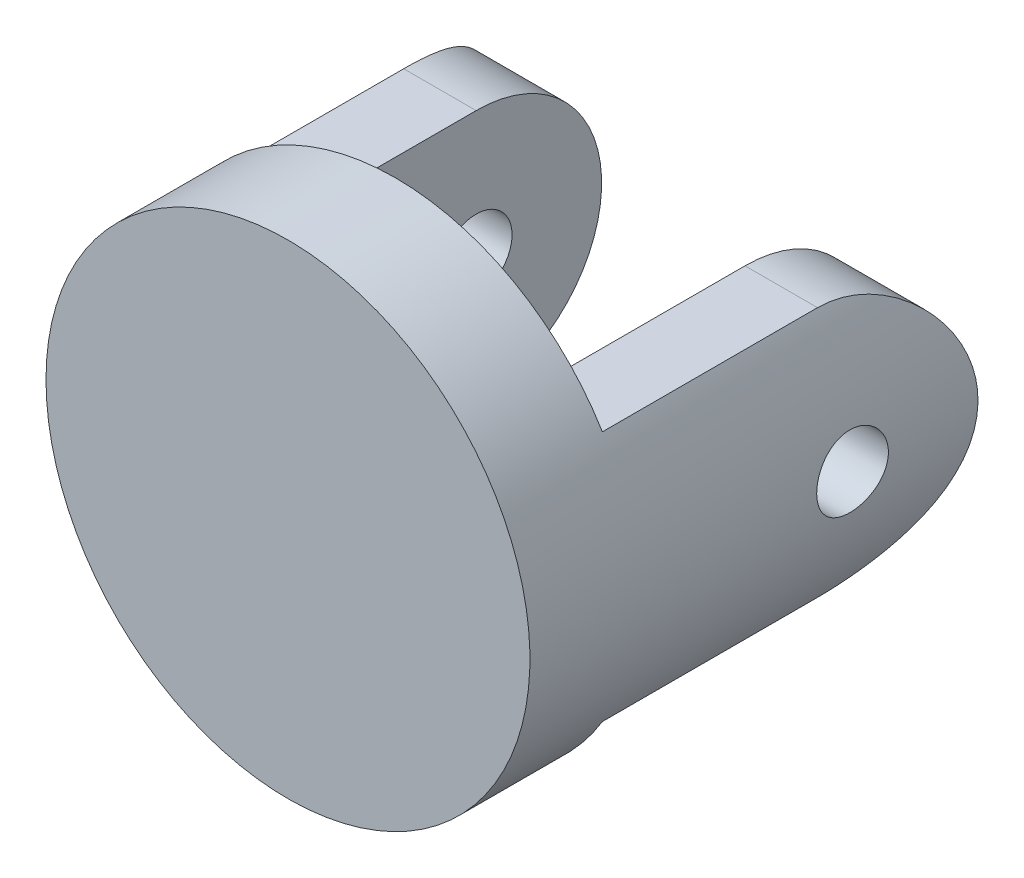
SolidWorks part; units mm, degrees
ref_plane "Front Plane" through (0, 0, 0) normal (0, 0, 1) x (1, 0, 0)
ref_plane "Top Plane" through (0, 0, 0) normal (0, 1, 0) x (1, 0, 0)
ref_plane "Right Plane" through (0, 0, 0) normal (1, 0, 0) x (0, 0, -1)
sketch "Sketch2" plane through (0, 0, 0) normal (0, 0, -1) x (-1, 0, 0)
  circle A0 centre (0, 0) radius 6.75
  dimension "D1" = 13.5
extrude "U Joint Base" add sketch "Sketch2" along normal blind 3
sketch "Sketch3" plane through (0, 0, -3) normal (0, 0, -1) x (-1, 0, 0)
  line L0 (-5.7717, 3.5) -> (-3.75, 3.5)
  line L1 (-3.75, 3.5) -> (-3.75, -3.5)
  line L2 (-3.75, -3.5) -> (-5.7717, -3.5)
  line L3 (3.75, -3.5) -> (3.75, 3.5)
  line L4 (3.75, 3.5) -> (5.7717, 3.5)
  line L5 (5.7717, -3.5) -> (3.75, -3.5)
  circle A0 centre (0, 0) radius 6.75 construction
  arc A1 (-5.7717, -3.5) -> (-5.7717, 3.5) centre (0, 0) cw
  arc A2 (5.7717, 3.5) -> (5.7717, -3.5) centre (0, 0) cw
  point P4 (-3.957, -3.4942)
  point P16 (0, 0)
  dimension "D2" = 7.5
  dimension "D3" = 7
  dimension "D1" = 2
extrude "U Joint Standups" add sketch "Sketch3" along normal blind 9.5
sketch "Sketch4" plane through (0, 0, 0) normal (1, 0, 0) x (0, 0, -1)
  line L0 (12.5, 3.5) -> (3, 3.5) construction
  line L1 (12.5, -3.5) -> (12.5, 3.5) construction
  line L2 (9, -3.5) -> (12.5, -3.5)
  line L3 (12.5, -3.5) -> (12.5, 0)
  line L4 (12.5, 0) -> (12.5, 3.5)
  line L5 (12.5, 3.5) -> (9, 3.5)
  line L6 (12.5, -3.5) -> (3, -3.5) construction
  arc A0 (12.5, 0) -> (9, 3.5) centre (9, 0) ccw
  arc A1 (9, -3.5) -> (12.5, 0) centre (9, 0) ccw
extrude "Standup Round" cut sketch "Sketch4" against normal through all both and the other way through all contours A1 L2 L3 | A0 L5 L4
sketch "Sketch5" plane through (0, 0, 0) normal (1, 0, 0) x (0, 0, -1)
  circle A0 centre (9, 0) radius 1
  dimension "D1" = 2
extrude "Ball Holes" cut sketch "Sketch5" against normal through all both and the other way through all
